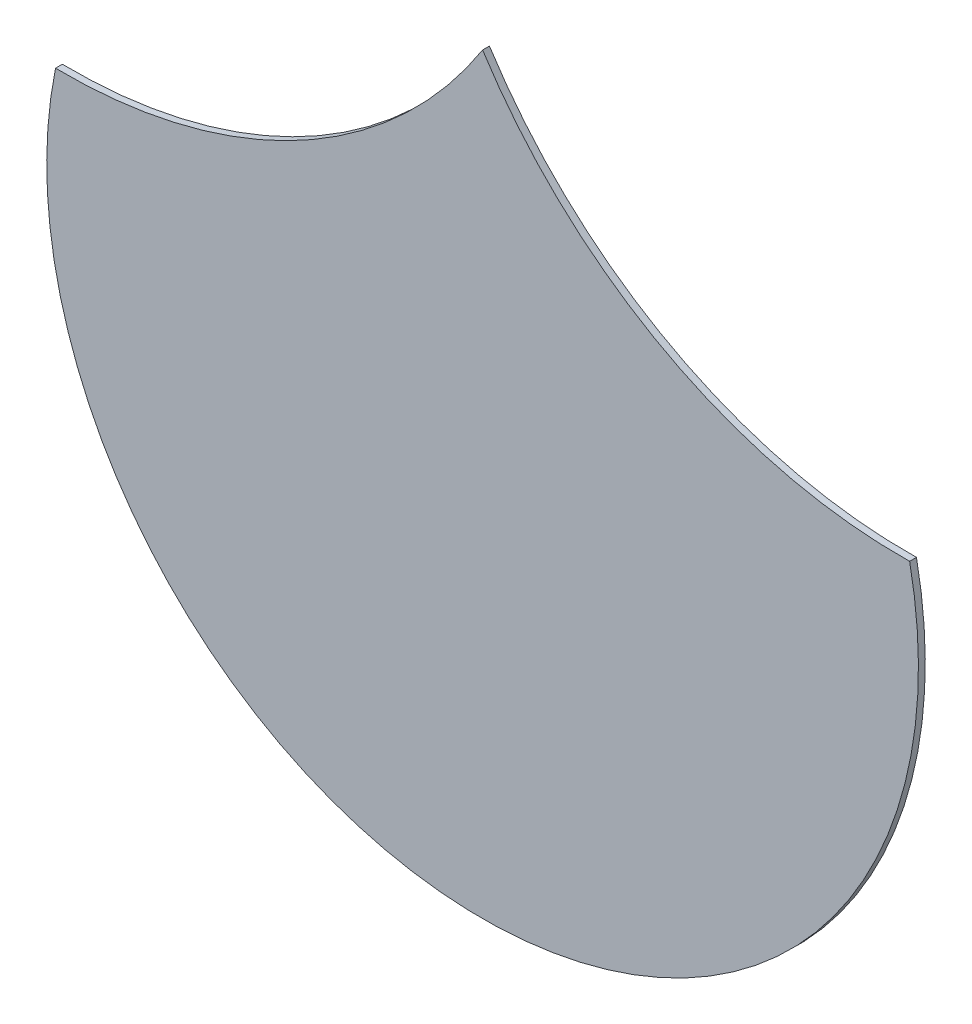
SolidWorks part; units mm, degrees
ref_plane "Alzado" through (0, 0, 0) normal (0, 0, 1) x (1, 0, 0)
ref_plane "Planta" through (0, 0, 0) normal (0, 1, 0) x (1, 0, 0)
ref_plane "Vista lateral" through (0, 0, 0) normal (1, 0, 0) x (0, 0, -1)
sketch "Model" plane through (0, 0, 0) normal (0, 0, 1) x (1, 0, 0)
  arc A0 (25.05, 16.6496) -> (37.55, 16.6496) centre (31.3, 15.3734) ccw
  arc A1 (25.05, 16.6496) -> (31.3, 20.0056) centre (25.1698, 23.9242) ccw
  arc A2 (31.3, 20.0056) -> (37.55, 16.6496) centre (37.4302, 23.9242) ccw
extrude "Saliente-Extruir1" add sketch "Model" along normal blind 0.1
